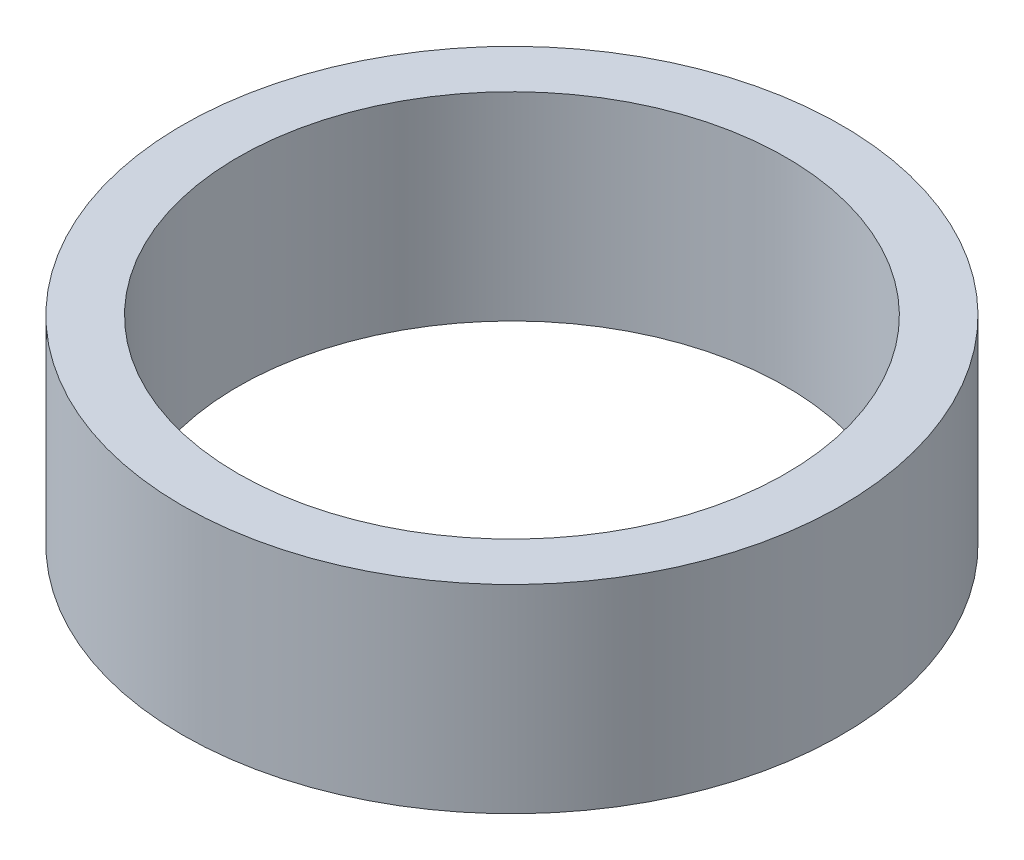
SolidWorks part; units mm, degrees
material "Alloy Steel"
ref_plane "Front Plane" through (0, 0, 0) normal (0, 0, 1) x (1, 0, 0)
ref_plane "Top Plane" through (0, 0, 0) normal (0, 1, 0) x (1, 0, 0)
ref_plane "Right Plane" through (0, 0, 0) normal (1, 0, 0) x (0, 0, -1)
sketch "Sketch1" plane through (0, 0, 0) normal (0, 1, 0) x (1, 0, 0)
  circle A0 centre (0, 0) radius 21.082
  circle A1 centre (0, 0) radius 17.526
  dimension "D1" = 42.164
  dimension "D2" = 35.052
extrude "Boss-Extrude1" add sketch "Sketch1" along normal blind 12.7
